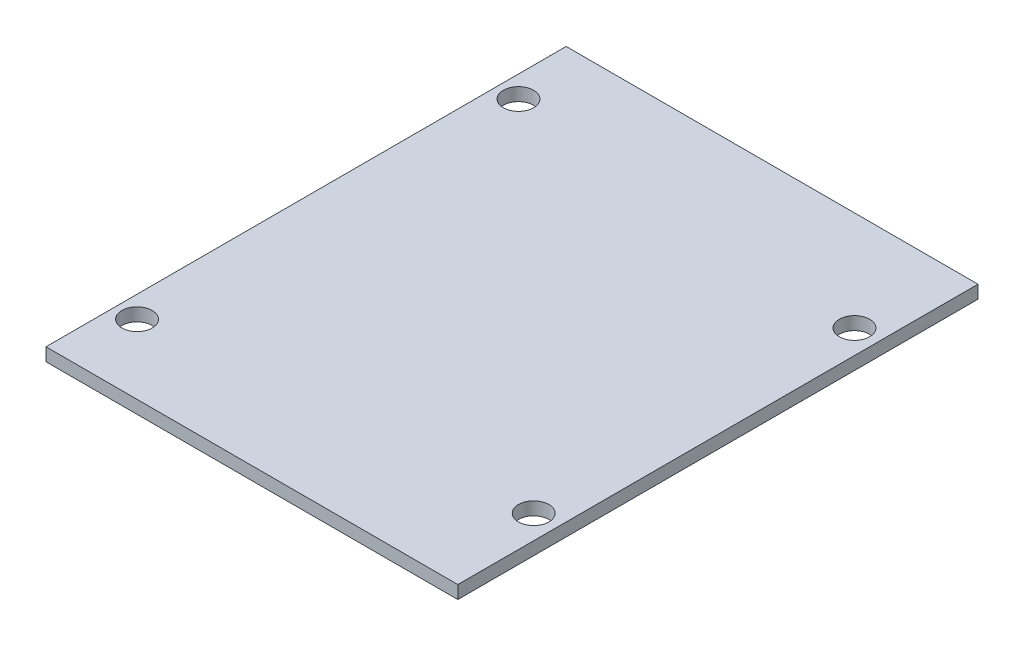
SolidWorks part; units mm, degrees
ref_plane "Front Plane" through (0, 0, 0) normal (0, 0, 1) x (1, 0, 0)
ref_plane "Top Plane" through (0, 0, 0) normal (0, 1, 0) x (1, 0, 0)
ref_plane "Right Plane" through (0, 0, 0) normal (1, 0, 0) x (0, 0, -1)
sketch "Sketch1" plane through (0, 0, 0) normal (0, 1, 0) x (1, 0, 0)
  line L1 (0, 0) -> (95, 0)
  line L2 (0, 0) -> (0, 120)
  line L3 (0, 120) -> (95, 120)
  line L4 (95, 0) -> (95, 120)
  dimension "D1" = 120
  dimension "D2" = 95
extrude "Boss-Extrude1" add sketch "Sketch1" along normal blind 3
sketch "Sketch2" plane through (0, 3, 0) normal (0, 1, 0) x (1, 0, 0)
  line L2 (0, 120) -> (0, 0) construction
  line L4 (0, 60) -> (95, 60) construction
  line L5 (95, 0) -> (95, 120) construction
  circle A1 centre (89.5, 23) radius 3.5
  circle A2 centre (5, 16) radius 3.5
  circle A4 centre (89.5, 97) radius 3.5
  circle A5 centre (5, 104) radius 3.5
  dimension "D1" = 88
  dimension "D2" = 7
  dimension "D3" = 7
  dimension "D5" = 74
  dimension "D6" = 84.5
  dimension "D9" = 5
extrude "Cut-Extrude1" cut sketch "Sketch2" against normal through all
sketch "Sketch3" plane through (0, 3, 0) normal (0, 1, 0) x (1, 0, 0)
  line L0 (0, 60) -> (95, 60) construction
  line L1 (0, 120) -> (0, 0) construction
  line L2 (95, 0) -> (95, 120) construction
sketch "Sketch5" plane through (0, 0, 0) normal (0, -1, 0) x (1, 0, 0)
  line L0 (0, -60) -> (95, -60) construction
  line L1 (0, -120) -> (0, 0) construction
  line L2 (95, 0) -> (95, -120) construction
